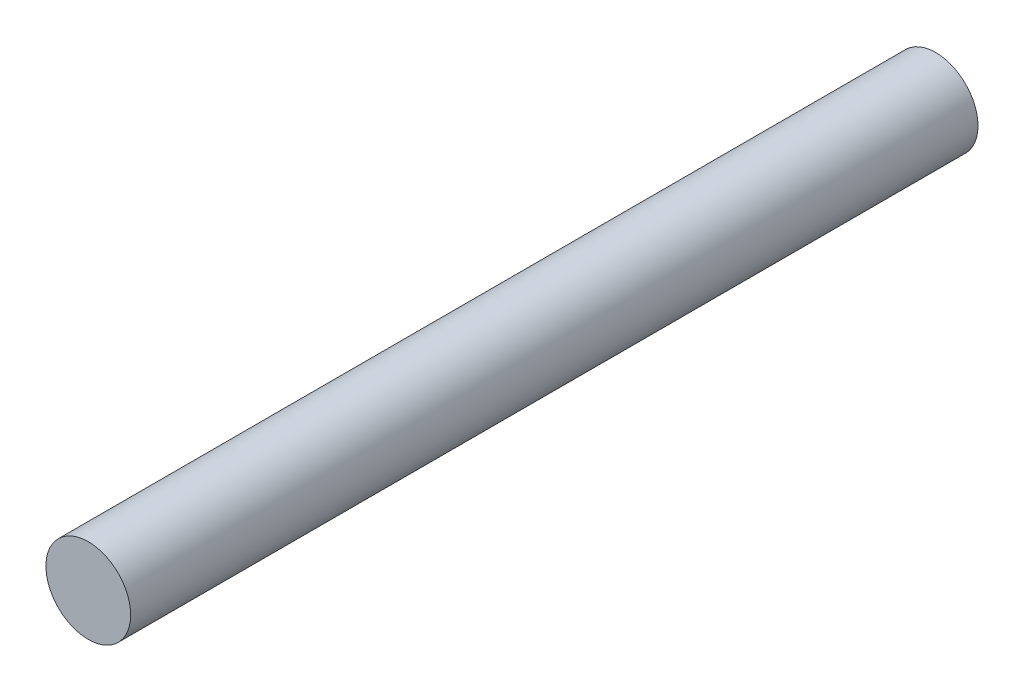
SolidWorks part; units mm, degrees
ref_plane "Front Plane" through (0, 0, 0) normal (0, 0, 1) x (1, 0, 0)
ref_plane "Top Plane" through (0, 0, 0) normal (0, 1, 0) x (1, 0, 0)
ref_plane "Right Plane" through (0, 0, 0) normal (1, 0, 0) x (0, 0, -1)
sketch "Sketch1" plane through (0, 0, 0) normal (0, 0, 1) x (1, 0, 0)
  circle A0 centre (0, 0) radius 7.62
  dimension "D1" = 15.24
extrude "Boss-Extrude1" add sketch "Sketch1" along normal blind 152.4
